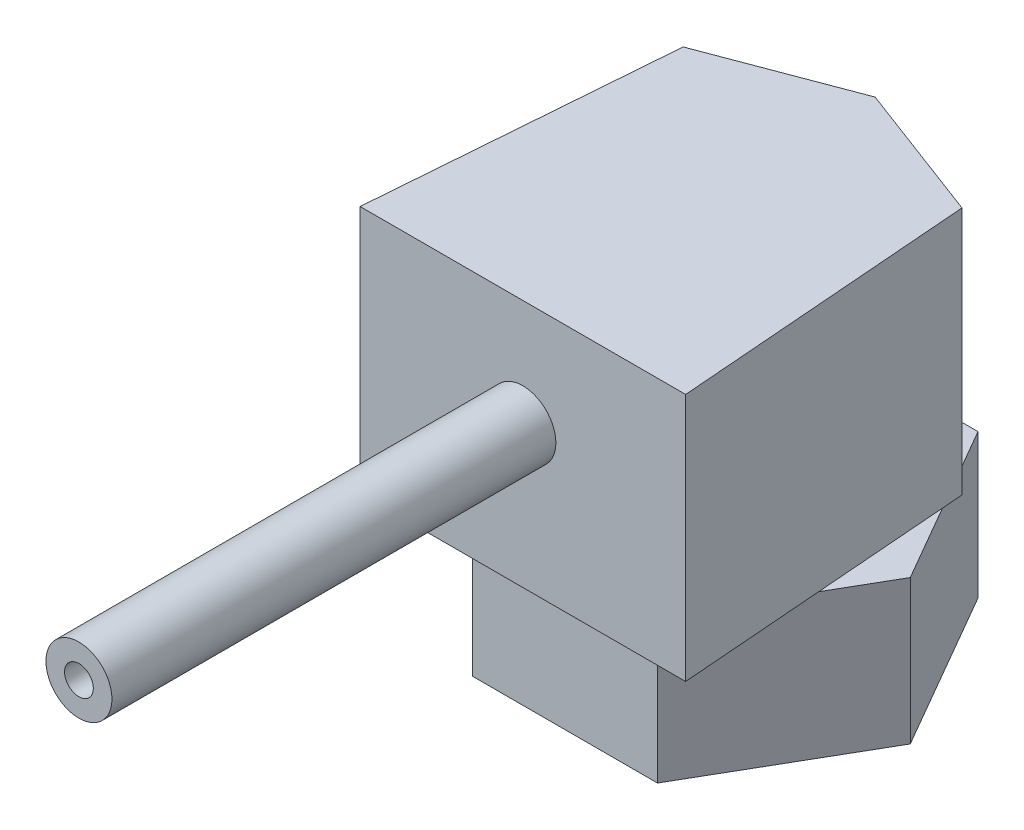
SolidWorks part; units mm, degrees
ref_plane "Front Plane" through (0, 0, 0) normal (0, 0, 1) x (1, 0, 0)
ref_plane "Top Plane" through (0, 0, 0) normal (0, 1, 0) x (1, 0, 0)
ref_plane "Right Plane" through (0, 0, 0) normal (1, 0, 0) x (0, 0, -1)
sketch "Sketch1" plane through (0, 0, 0) normal (0, 1, 0) x (1, 0, 0)
  line L1 (6.2527, 0) -> (3.1264, 5.415)
  line L2 (3.1264, 5.415) -> (-3.1264, 5.415)
  line L3 (-3.1264, 5.415) -> (-6.2527, 0)
  line L4 (-6.2527, 0) -> (-3.1264, -5.415)
  line L5 (-3.1264, -5.415) -> (3.1264, -5.415)
  line L6 (3.1264, -5.415) -> (6.2527, 0)
  circle A0 centre (0, 0) radius 5.415 construction
  dimension "D1" = 10.83
extrude "Boss-Extrude1" add sketch "Sketch1" along normal blind 4.87
sketch "Sketch2" plane through (0, 4.87, 0) normal (0, 1, 0) x (1, 0, 0)
  line L0 (0, 5.0658) -> (-4.7103, 3.2896)
  line L1 (-4.7103, 3.2896) -> (-5.5, -6.8373)
  line L2 (-5.5, -6.8373) -> (-1.5285, -6.8373)
  line L3 (0, 0) -> (0, 7.4509) construction
  line L4 (5.5, -6.8373) -> (-1.5285, -6.8373)
  line L5 (4.7103, 3.2896) -> (5.5, -6.8373)
  line L6 (0, 5.0658) -> (4.7103, 3.2896)
  dimension "D1" = 11
extrude "Boss-Extrude2" add sketch "Sketch2" along normal blind 8.4
sketch "Sketch3" plane through (0, 0, 6.8373) normal (0, 0, 1) x (1, 0, 0)
  line L1 (-3.1264, 0) -> (3.1264, 0) construction
  circle A0 centre (0, 9.66) radius 0.4858
  circle A1 centre (0, 9.66) radius 1.115
  dimension "D1" = 2.23
  dimension "D2" = 9.66
extrude "Boss-Extrude3" add sketch "Sketch3" along normal blind 15
sketch "Sketch4" plane through (0, 0, 0) normal (0, -1, 0) x (1, 0, 0)
  circle A0 centre (0, 0) radius 2.8864
extrude "Boss-Extrude4" add sketch "Sketch4" along normal blind 0.5
